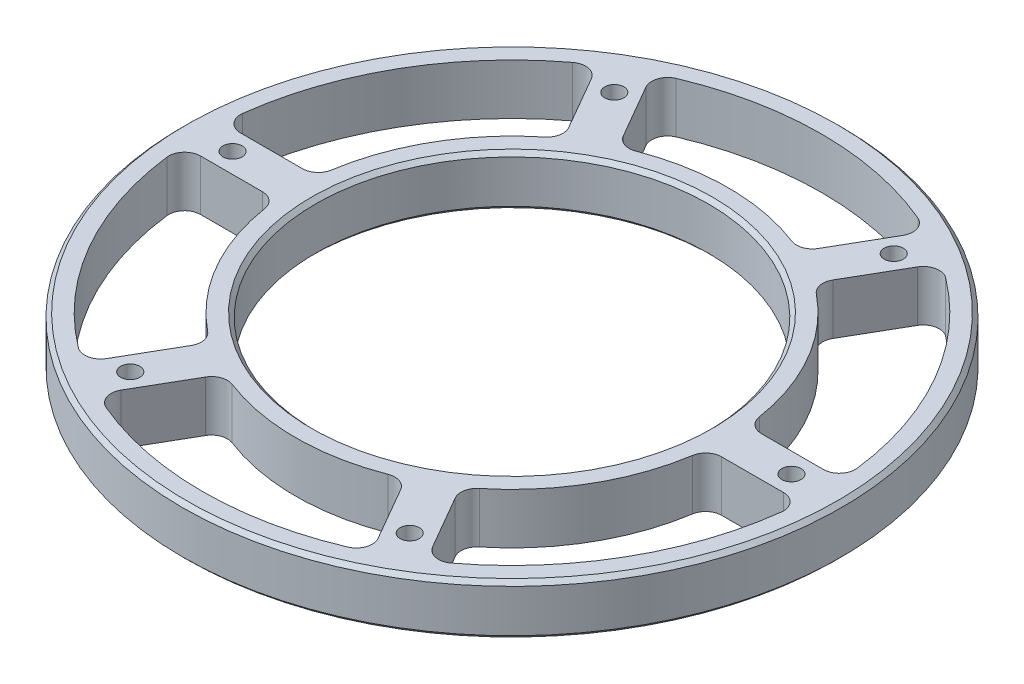
SolidWorks part; units mm, degrees
material "6061-T6 (SS)"
ref_plane "Front Plane" through (0, 0, 0) normal (0, 0, 1) x (1, 0, 0)
ref_plane "Top Plane" through (0, 0, 0) normal (0, 1, 0) x (1, 0, 0)
ref_plane "Right Plane" through (0, 0, 0) normal (1, 0, 0) x (0, 0, -1)
sketch "Sketch2" plane through (0, 0, 0) normal (1, 0, 0) x (0, 0, -1)
  line L0 (-49.2125, 0) -> (-82.55, 0)
  line L1 (-82.55, 0) -> (-82.55, 12.7)
  line L2 (-82.55, 12.7) -> (-49.2125, 12.7)
  line L3 (-49.2125, 12.7) -> (-49.2125, 0)
  dimension "D1" = 82.55
  dimension "D2" = 12.7
  dimension "D4" = 49.2125
ref_axis "Axis1" through (0, -0.635, 0) along (0, 1, 0)
revolve "Revolve1" add sketch "Sketch2" angle 360 about axis through (0, -0.635, 0) along (0, 1, 0)
hole_wizard "#12 (0.189) Diameter Hole1" positions "Sketch6" profile "Sketch7" hole size "#12" standard "ANSI Inch" end condition through all
sketch "Sketch6" plane through (0, 12.7, 0) normal (0, 1, 0) x (1, 0, 0)
  line L0 (0, 0) -> (-69.8201, 120.932) construction
  line L2 (0, 0) -> (0, 109.0908) construction
  point P0 (-35, 60.6218)
  dimension "D1" = 30
  dimension "D2" = 70
sketch "Sketch7" plane through (-35, 12.7, -60.6218) normal (1, 0, 0) x (0, 0, 1)
  line L0 (0, 0) -> (0, 12.7)
  line L1 (0, 12.7) -> (2.4003, 12.7)
  line L2 (2.4003, 12.7) -> (2.4003, 0)
  line L5 (2.4003, 0) -> (0, 0)
  line L11 (0, -6.35) -> (0, 107.95) construction
  dimension "Thru Hole Dia." = 4.8006
  dimension "Thru Hole Depth" = 12.7
pattern_circular "CirPattern3" count 6 over 360 about axis through (0, 0, 0) along (0, 1, 0) of "#12 (0.189) Diameter Hole1"
sketch "Sketch8" plane through (0, 12.7, 0) normal (0, 1, 0) x (1, 0, 0)
  line L4 (0, 0) -> (0, 93.9995) construction
  line L5 (-22.6606, 49.2493) -> (-34.3642, 69.5205)
  line L6 (22.6606, 49.2493) -> (34.3642, 69.5205)
  line L7 (0, 0) -> (-35, 60.6218) construction
  arc A0 (-22.6606, 49.2493) -> (22.6606, 49.2493) centre (0, 0) cw
  arc A1 (-34.3642, 69.5205) -> (34.3642, 69.5205) centre (0, 0) cw
  circle A2 centre (0, 0) radius 82.55 construction
  circle A4 centre (0, 0) radius 49.2125 construction
  dimension "D1" = 5
  dimension "D2" = 5
  dimension "D3" = 5
extrude "Cut-Extrude1" cut sketch "Sketch8" against normal through all
fillet "Fillet1" radius 4 4 edges at (-22.6606, 6.35, -49.2493) (22.6606, 6.35, -49.2493) (34.3642, 6.35, -69.5205) (-34.3642, 6.35, -69.5205)
pattern_circular "CirPattern4" count 6 over 360 about axis through (0, 0, 0) along (0, 1, 0) of "Cut-Extrude1", "Fillet1"
chamfer "Chamfer1" distance 1 angle 45 2 edges at (0, 12.7, -49.2125) (0, 0, -49.2125)
chamfer "Chamfer2" distance 1 angle 45 2 edges at (0, 12.7, -82.55) (0, 0, -82.55)
equation "\"TubeDiameter\" = 6.500in"
equation "\"D1@Sketch2\"=\"TubeDiameter\"/2"
